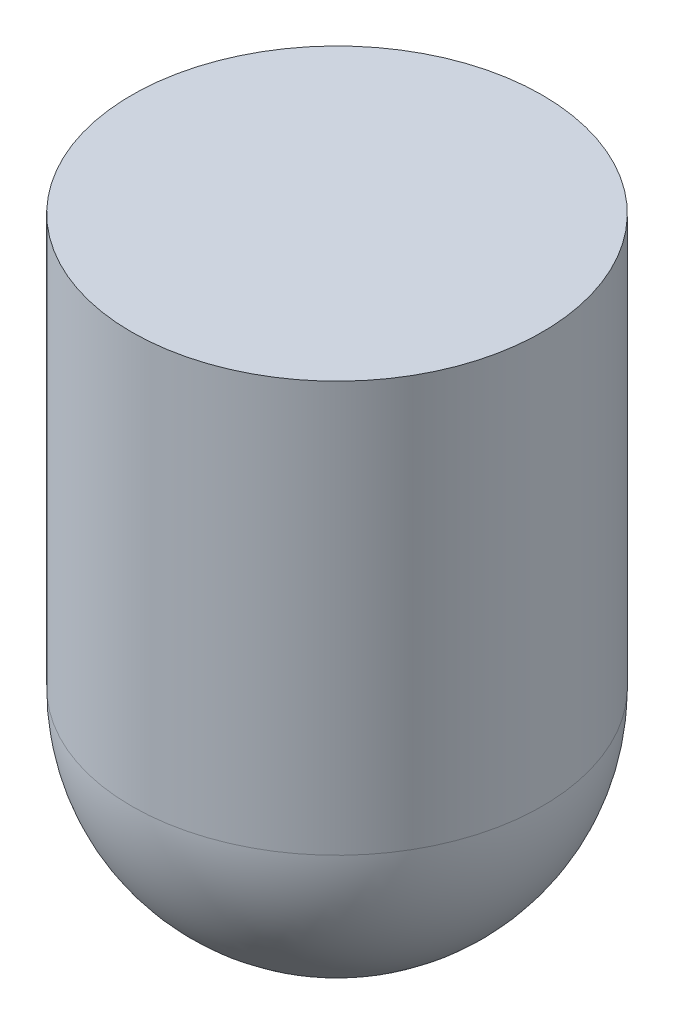
SolidWorks part; units mm, degrees
ref_plane "Front Plane" through (0, 0, 0) normal (0, 0, 1) x (1, 0, 0)
ref_plane "Top Plane" through (0, 0, 0) normal (0, 1, 0) x (1, 0, 0)
ref_plane "Right Plane" through (0, 0, 0) normal (1, 0, 0) x (0, 0, -1)
sketch "Sketch1" plane through (0, 0, 0) normal (0, 1, 0) x (1, 0, 0)
  circle A0 centre (0, 0) radius 50
extrude "Boss-Extrude1" add sketch "Sketch1" along normal blind 100
sketch "Sketch2" plane through (0, 0, 0) normal (1, 0, 0) x (0, 0, -1)
  line L0 (-50, 0) -> (50, 0) construction
  line L1 (-50, 0) -> (0, 0)
  line L2 (0, 0) -> (0, -50)
  arc A0 (-50, 0) -> (0, -50) centre (0, 0) ccw
revolve "Revolve1" add sketch "Sketch2" angle 360 about L2
